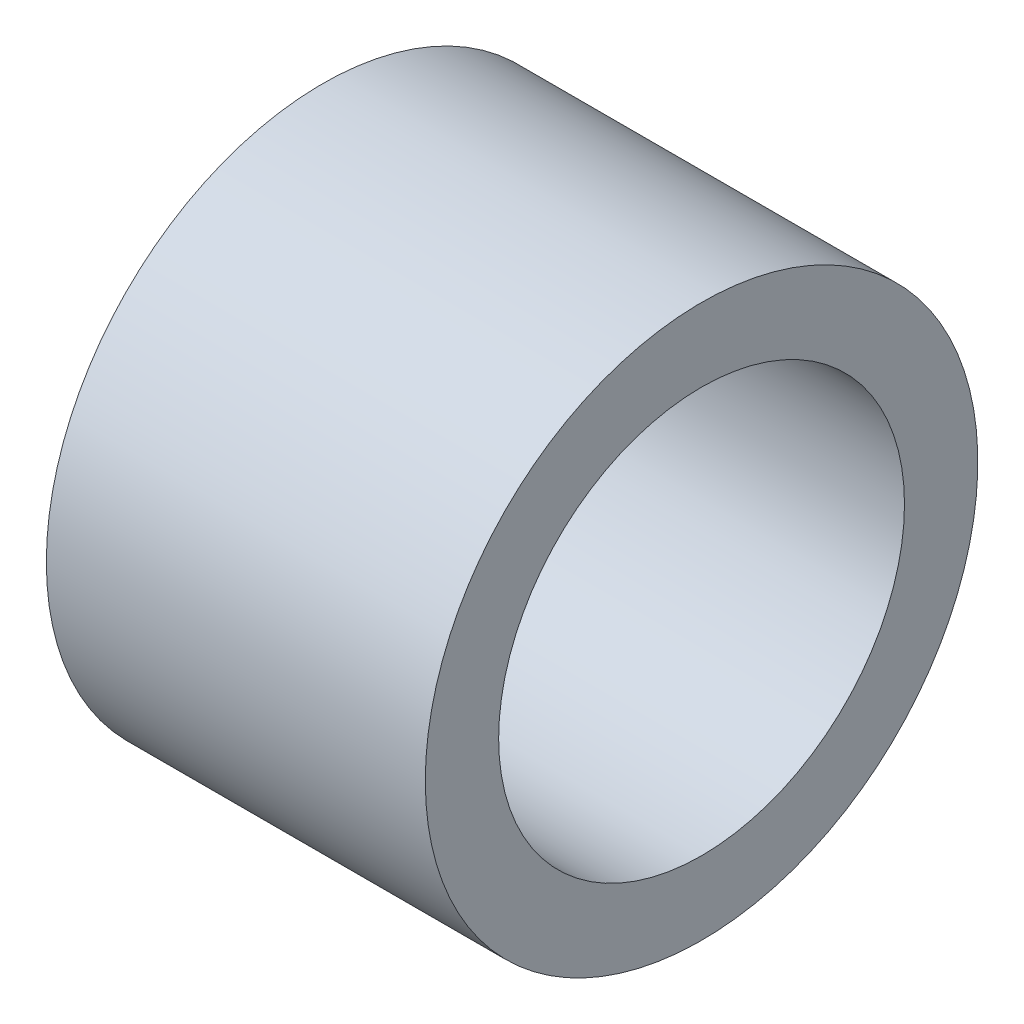
SolidWorks part; units mm, degrees
material "ABS"
ref_plane "Front Plane" through (0, 0, 0) normal (0, 0, 1) x (1, 0, 0)
ref_plane "Top Plane" through (0, 0, 0) normal (0, 1, 0) x (1, 0, 0)
ref_plane "Right Plane" through (0, 0, 0) normal (1, 0, 0) x (0, 0, -1)
sketch "Sketch1" plane through (0, 0, 0) normal (0, 1, 0) x (1, 0, 0)
  line L0 (0, 0) -> (22.4144, 0) construction
  line L1 (0, 0) -> (7.75, 0)
  line L2 (0, 0) -> (0, -4.15)
  line L3 (0, -4.15) -> (7.75, -4.15)
  line L4 (7.75, 0) -> (7.75, -4.15)
  line L5 (0, 0) -> (7.75, 0)
  line L6 (0, 0) -> (0, -5.65)
  line L7 (0, -5.65) -> (7.75, -5.65)
  line L8 (7.75, 0) -> (7.75, -5.65)
  dimension "D1" = 7.75
  dimension "D2" = 4.15
  dimension "D3" = 1.5
revolve "Revolve1" add sketch "Sketch1" angle 360 about L0
